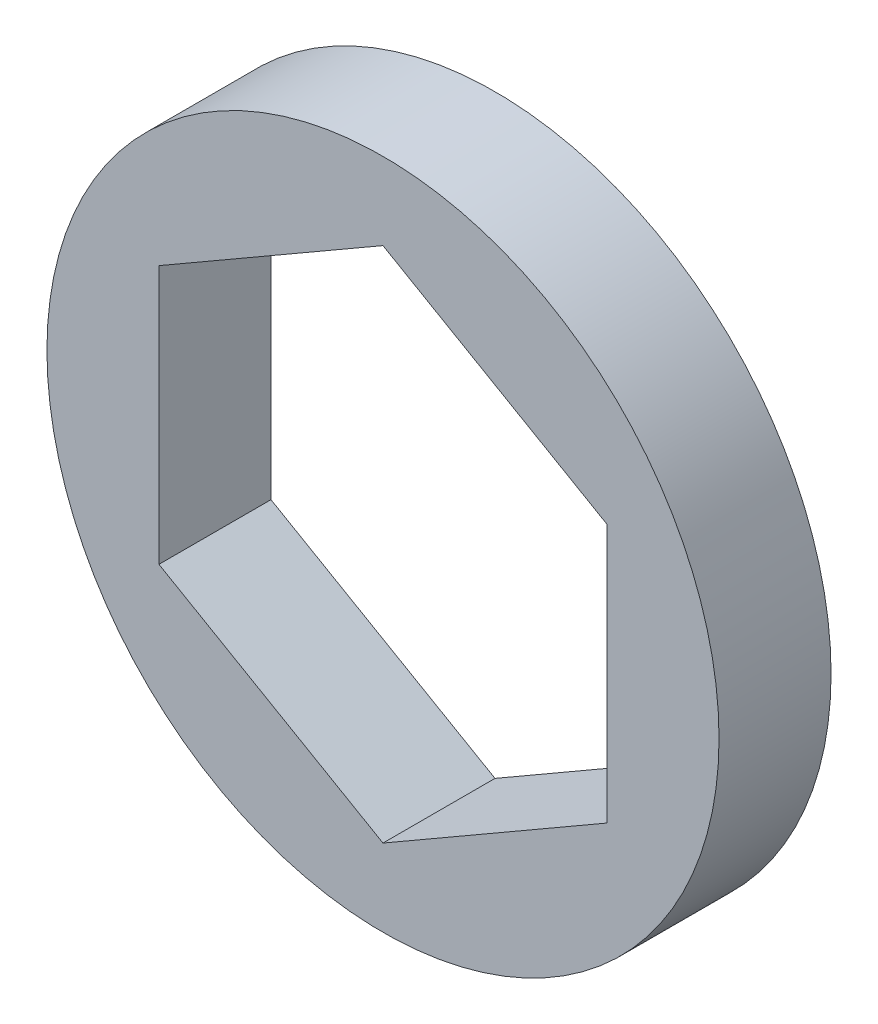
SolidWorks part; units mm, degrees
ref_plane "Front Plane" through (0, 0, 0) normal (0, 0, 1) x (1, 0, 0)
ref_plane "Top Plane" through (0, 0, 0) normal (0, 1, 0) x (1, 0, 0)
ref_plane "Right Plane" through (0, 0, 0) normal (1, 0, 0) x (0, 0, -1)
sketch "Sketch1" plane through (0, 0, 0) normal (0, 0, 1) x (1, 0, 0)
  line L1 (0, 14.6647) -> (-12.7, 7.3323)
  line L2 (-12.7, 7.3323) -> (-12.7, -7.3323)
  line L3 (-12.7, -7.3323) -> (0, -14.6647)
  line L4 (0, -14.6647) -> (12.7, -7.3323)
  line L5 (12.7, -7.3323) -> (12.7, 7.3323)
  line L6 (12.7, 7.3323) -> (0, 14.6647)
  circle A0 centre (0, 0) radius 12.7 construction
  circle A1 centre (0, 0) radius 19.05
  dimension "D1" = 38.1
  dimension "D2" = 25.4
extrude "Boss-Extrude1" add sketch "Sketch1" along normal mid plane 6.35
